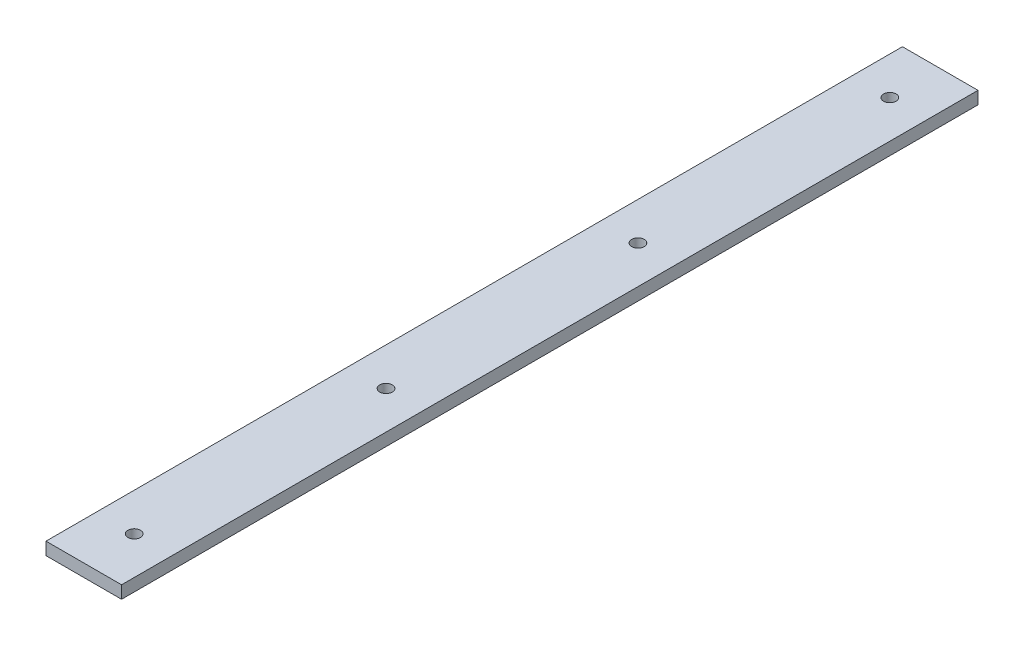
SolidWorks part; units mm, degrees
material "AISI 1045 Steel, cold drawn"
ref_plane "Front Plane" through (0, 0, 0) normal (0, 0, 1) x (1, 0, 0)
ref_plane "Top Plane" through (0, 0, 0) normal (0, 1, 0) x (1, 0, 0)
ref_plane "Right Plane" through (0, 0, 0) normal (1, 0, 0) x (0, 0, -1)
sketch "Sketch1" plane through (0, 0, 0) normal (0, 0, 1) x (1, 0, 0)
  line L1 (-15, 2.5) -> (15, 2.5)
  line L2 (-15, 2.5) -> (-15, -2.5)
  line L3 (-15, -2.5) -> (15, -2.5)
  line L4 (15, 2.5) -> (15, -2.5)
  point P4 (15, 0)
  point P6 (0, 2.5)
  dimension "D1" = 30
  dimension "D2" = 5
extrude "Boss-Extrude1" add sketch "Sketch1" along normal mid plane 340
sketch "Sketch2" plane through (0, 2.5, 0) normal (0, 1, 0) x (1, 0, 0)
  circle A0 centre (0, 87.5) radius 4
  circle A1 centre (0, 0) radius 4
  circle A2 centre (0, -87.5) radius 4
  circle A3 centre (0, -87.5) radius 4 construction
  circle A4 centre (0, 87.5) radius 4 construction
  dimension "D1" = 8
extrude "Holes for 20mm strip ONLY" [suppressed] cut sketch "Sketch2" against normal through all
sketch "Sketch3" plane through (0, 2.5, 0) normal (0, 1, 0) x (1, 0, 0)
  line L0 (0, 0) -> (65.8821, 0) construction
  line L1 (15, -170) -> (-15, -170) construction
  circle A0 centre (0, -50) radius 2.5
  circle A1 centre (0, -150) radius 2.5
  circle A2 centre (0, 150) radius 2.5
  circle A3 centre (0, 50) radius 2.5
  point P7 (0, -170)
  dimension "D2" = 5
  dimension "D1" = 100
  dimension "D3" = 300
extrude "Cut-Extrude1" cut sketch "Sketch3" against normal through all
